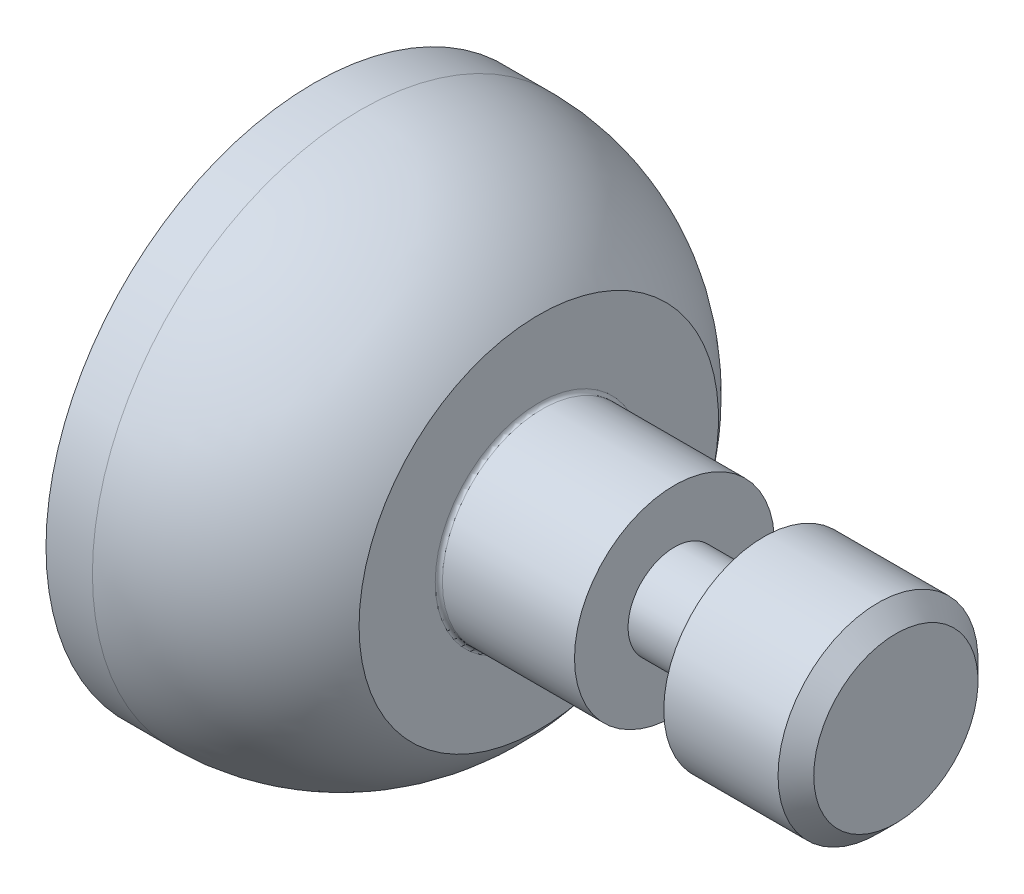
SolidWorks part; units mm, degrees
ref_plane "Front Plane" through (0, 0, 0) normal (0, 0, 1) x (1, 0, 0)
ref_plane "Top Plane" through (0, 0, 0) normal (0, 1, 0) x (1, 0, 0)
ref_plane "Right Plane" through (0, 0, 0) normal (1, 0, 0) x (0, 0, -1)
sketch "Sketch1" plane through (0, 0, 0) normal (0, 0, 1) x (1, 0, 0)
  line L0 (-1.6953, 0) -> (2.8939, 0) construction
  line L1 (0, 0) -> (0, 0.75)
  line L2 (0, 0.75) -> (0.13, 0.75)
  line L4 (0.63, 0.5033) -> (0.63, 0.28)
  line L5 (0.63, 0.28) -> (1.01, 0.28)
  line L6 (1.01, 0.28) -> (1.01, 0.13)
  line L7 (1.01, 0.13) -> (1.26, 0.13)
  line L8 (1.26, 0.13) -> (1.26, 0.28)
  line L9 (1.26, 0.28) -> (1.63, 0.28)
  line L10 (1.63, 0.28) -> (1.63, 0)
  line L11 (1.63, 0) -> (0, 0)
  arc A1 (0.63, 0.5033) -> (0.13, 0.75) centre (0.13, 0.12) ccw
  point P16 (0.13, 0.13)
  point P17 (0, 0)
  point P18 (0, 0)
  point P19 (0.13, 0.0934)
  point P20 (0.13, 0.1459)
  dimension "D9" = 0.63
  dimension "D10" = 0.5033
  dimension "D1" = 0.63
  dimension "D2" = 0.75
  dimension "D3" = 0.28
  dimension "D4" = 0.28
  dimension "D5" = 0.13
  dimension "D6" = 0.13
  dimension "D7" = 0.25
  dimension "D8" = 0.38
  dimension "D11" = 0.15
  dimension "D12" = 1
revolve "Revolve1" add sketch "Sketch1" angle 360 about L0
fillet "Fillet1" radius 0.01 1 edges at (0.63, 0, 0.28)
chamfer "Chamfer1" distance 0.05 angle 45 1 edges at (1.63, 0, 0.28)
